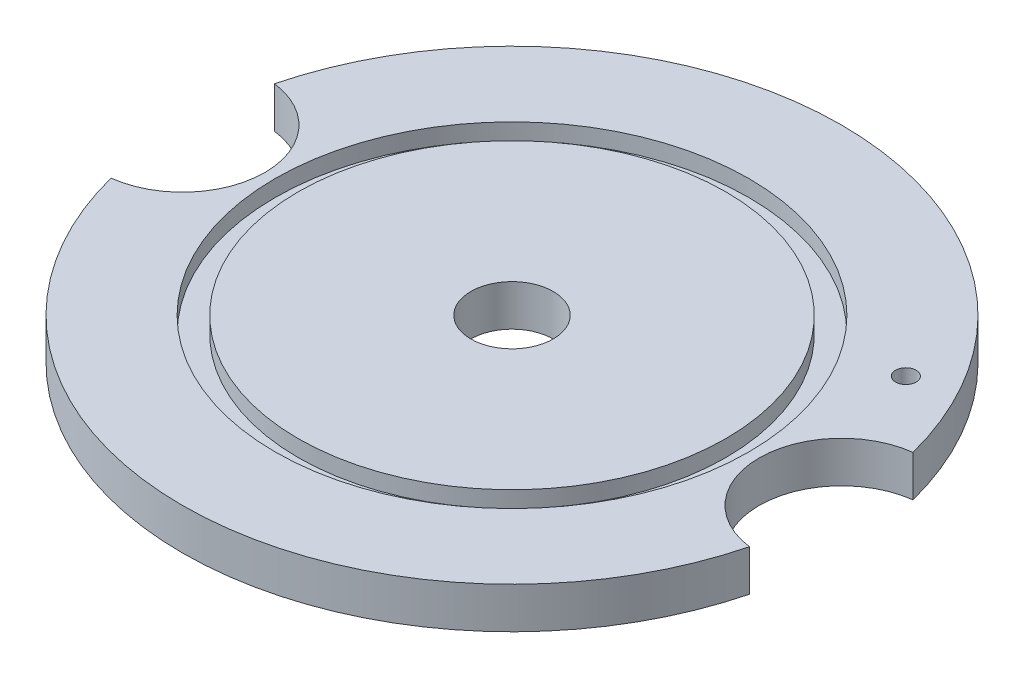
SolidWorks part; units mm, degrees
ref_plane "Front Plane" through (0, 0, 0) normal (0, 0, 1) x (1, 0, 0)
ref_plane "Top Plane" through (0, 0, 0) normal (0, 1, 0) x (1, 0, 0)
ref_plane "Right Plane" through (0, 0, 0) normal (1, 0, 0) x (0, 0, -1)
sketch "Sketch1" plane through (0, 0, 0) normal (0, 0, 1) x (1, 0, 0)
  line L0 (-32.9565, 6.35) -> (-32.9565, 3.81)
  line L1 (0, 0) -> (-50.8, 0)
  line L2 (0, 0) -> (0, 6.35)
  line L3 (0, 6.35) -> (-32.9565, 6.35)
  line L4 (-50.8, 0) -> (-50.8, 6.35)
  line L5 (-32.9565, 3.81) -> (-36.5125, 3.81)
  line L6 (-36.5125, 3.81) -> (-36.5125, 6.35)
  line L7 (-36.5125, 6.35) -> (-50.8, 6.35)
  dimension "D1" = 6.35
  dimension "D2" = 50.8
  dimension "D3" = 2.54
  dimension "D4" = 3.556
  dimension "D5" = 32.9565
revolve "Revolve1" add sketch "Sketch1" angle 360 about L2
hole_wizard "1/2 (0.5) Diameter Hole1" positions "Sketch2" profile "Sketch3" hole size "1/2" standard "ANSI Inch" end condition through all
sketch "Sketch2" plane through (0, 6.35, 0) normal (0, 1, 0) x (1, 0, 0)
  point P0 (0, 0)
sketch "Sketch3" plane through (0, 6.35, 0) normal (1, 0, 0) x (0, 0, 1)
  line L0 (0, 0) -> (0, 6.35)
  line L1 (0, 6.35) -> (6.35, 6.35)
  line L2 (6.35, 6.35) -> (6.35, 0)
  line L5 (6.35, 0) -> (0, 0)
  line L11 (0, -6.35) -> (0, 107.95) construction
  dimension "Thru Hole Dia." = 12.7
  dimension "Thru Hole Depth" = 6.35
hole_wizard "1 (1) Diameter Hole1" positions "Sketch4" profile "Sketch6" hole size "1" standard "ANSI Inch" end condition through all
sketch "Sketch4" plane through (0, 6.35, 0) normal (0, 1, 0) x (1, 0, 0)
  circle A0 centre (0, 0) radius 50.8 construction
  point P0 (50.8, 0)
  point P5 (-50.8, 0)
  point P9 (0, 0)
sketch "Sketch6" plane through (50.8, 6.35, 0) normal (1, 0, 0) x (0, 0, 1)
  line L0 (0, 0) -> (0, 6.35)
  line L1 (0, 6.35) -> (12.7, 6.35)
  line L2 (12.7, 6.35) -> (12.7, 0)
  line L5 (12.7, 0) -> (0, 0)
  line L11 (0, -6.35) -> (0, 107.95) construction
  dimension "Thru Hole Dia." = 25.4
  dimension "Thru Hole Depth" = 6.35
hole_wizard "1/8 (0.125) Diameter Hole1" positions "Sketch7" profile "Sketch8" hole size "1/8" standard "ANSI Inch" end condition through all
sketch "Sketch7" plane through (0, 6.35, 0) normal (0, 1, 0) x (1, 0, 0)
  line L0 (-0.6799, 0) -> (49.9279, 0) construction
  line L2 (38.4948, 22.225) -> (0, 0) construction
  point P0 (38.4948, 22.225)
  dimension "D1" = 44.45
  dimension "D2" = 30
sketch "Sketch8" plane through (38.4948, 6.35, -22.225) normal (1, 0, 0) x (0, 0, 1)
  line L0 (0, 0) -> (0, 6.35)
  line L1 (0, 6.35) -> (1.5875, 6.35)
  line L2 (1.5875, 6.35) -> (1.5875, 0)
  line L5 (1.5875, 0) -> (0, 0)
  line L11 (0, -6.35) -> (0, 107.95) construction
  dimension "Thru Hole Dia." = 3.175
  dimension "Thru Hole Depth" = 6.35
